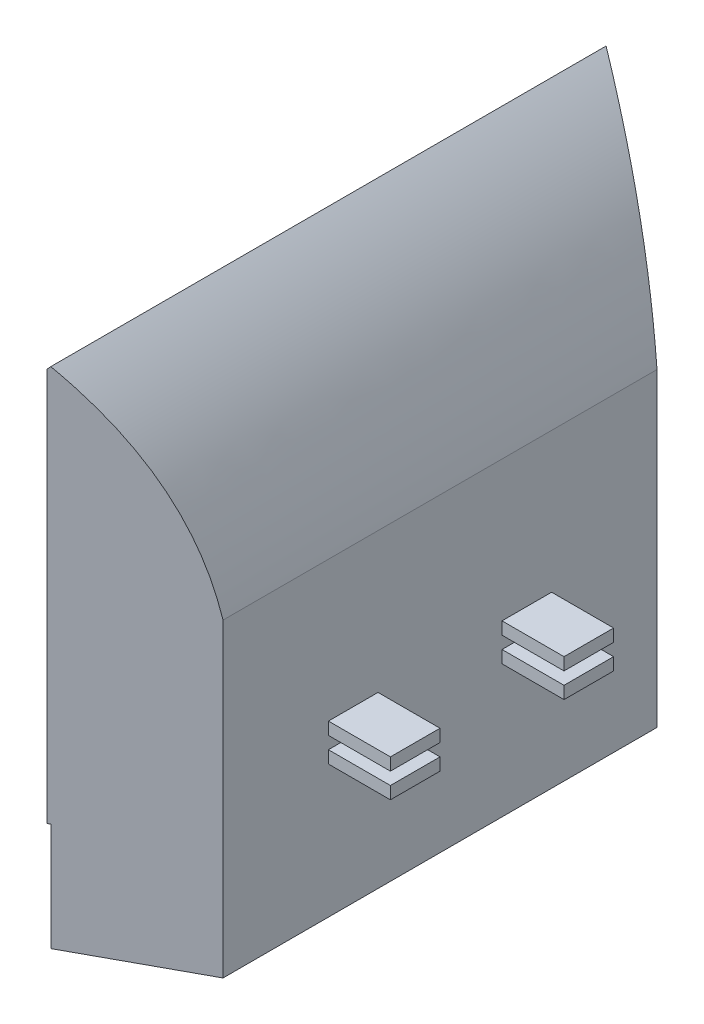
SolidWorks part; units mm, degrees
material "Pine"
ref_plane "Front Plane" through (0, 0, 0) normal (0, 0, 1) x (1, 0, 0)
ref_plane "Top Plane" through (0, 0, 0) normal (0, 1, 0) x (1, 0, 0)
ref_plane "Right Plane" through (0, 0, 0) normal (1, 0, 0) x (0, 0, -1)
sketch "Sketch1" plane through (0, 0, 0) normal (0, 0, 1) x (1, 0, 0)
  line L0 (0, 0) -> (0, -86.95)
  line L1 (0, -86.95) -> (90, -86.95)
  line L2 (90, -86.95) -> (90, 163.05)
  line L3 (3, 0) -> (3, -83.95)
  line L4 (3, -83.95) -> (87, -83.95)
  line L5 (87, -83.95) -> (87, 162.768)
  line L6 (0, 319.5362) -> (-1.9712, 317.2747)
  line L7 (0, 0) -> (3, 0)
  spline S0 degree 2 poles (90, 163.05) (72.3174, 256.4994) (0, 319.5362) knots 0 0 0 1 1 1
  spline S1 degree 1 poles (87, 162.768) (-1.9712, 317.2747) knots 0 0 1 1 construction
  spline S2 degree 3 poles (87, 162.768) (86.6353, 164.6855) (85.8667, 168.5225) (84.1938, 176.0942) (81.8385, 185.4174) (78.5926, 196.3641) (73.7046, 210.6444) (66.5448, 227.9027) (56.2723, 247.6718) (44.3168, 266.5051) (32.9484, 281.4235) (23.0079, 292.8943) (15.1298, 301.2651) (8.2091, 308.0497) (2.4655, 313.3571) (-0.4865, 315.9805) (-1.9712, 317.2747) knots 0.00149 0.00149 0.00149 0.00149 0.032694 0.063897 0.126304 0.188711 0.251118 0.375931 0.500745 0.625559 0.750373 0.812779 0.875186 0.937593 0.968797 1 1 1 1
  dimension "D4" = 184.0681
  dimension "D1" = 86.95
  dimension "D2" = 90
  dimension "D3" = 250
  dimension "D5" = 319.5362
  dimension "D6" = 3
extrude "Boss-Extrude1" add sketch "Sketch1" along normal blind 450
sketch "Sketch2" plane through (0, 0, 0) normal (0, 1, 0) x (1, 0, 0)
  line L0 (-1.9712, -450) -> (90, -400)
  line L1 (90, -450) -> (90, 0) construction
  line L2 (-1.9712, -450) -> (90, -450)
  line L3 (90, -450) -> (90, -400)
  line L4 (0, -225) -> (90, -225) construction
  line L5 (0, -450) -> (0, 0) construction
  line L6 (90, 0) -> (90, -50)
  line L7 (-1.9712, 0) -> (90, 0)
  line L8 (-1.9712, 0) -> (90, -50)
  dimension "D1" = 50
extrude "Cut-Extrude1" cut sketch "Sketch2" against normal through all both and the other way through all contours L6 L8 L7 | L3 L0 L2
sketch "Sketch3" plane through (0, 0, 0) normal (0, 1, 0) x (1, 0, 0)
  line L0 (-1.9712, -446) -> (90, -396)
  line L1 (-1.9712, -450) -> (-1.9712, 0) construction
  line L2 (90, -400) -> (90, -50) construction
  line L3 (-1.9712, -446) -> (-1.9712, -450)
  line L4 (-1.9712, -450) -> (90, -400)
  line L5 (90, -400) -> (90, -396)
  line L6 (90, -225) -> (-1.9712, -225) construction
  line L7 (-1.9712, -4) -> (-1.9712, 0)
  line L8 (90, -50) -> (90, -54)
  line L9 (-1.9712, 0) -> (90, -50)
  line L10 (-1.9712, -4) -> (90, -54)
  dimension "D1" = 4
  dimension "D2" = 4
extrude "Boss-Extrude2" add sketch "Sketch3" along normal up to next and the other way up to next
sketch "Sketch4" plane through (90, 0, 0) normal (1, 0, 0) x (0, 0, -1)
  line L0 (-225, -86.95) -> (-225, 105.8079) construction
  line L1 (-400, -86.95) -> (-50, -86.95) construction
  line L2 (-275, 30) -> (-315, 30)
  line L3 (-175, 40) -> (-135, 40)
  line L4 (-175, 40) -> (-175, 50)
  line L5 (-175, 50) -> (-135, 50)
  line L6 (-135, 40) -> (-135, 50)
  line L7 (-175, 40) -> (-135, 50) construction
  line L8 (-175, 50) -> (-135, 40) construction
  line L9 (-175, 20) -> (-135, 20)
  line L10 (-175, 20) -> (-175, 30)
  line L11 (-175, 30) -> (-135, 30)
  line L12 (-135, 20) -> (-135, 30)
  line L13 (-175, 20) -> (-135, 30) construction
  line L14 (-175, 30) -> (-135, 20) construction
  line L15 (-315, 20) -> (-315, 30)
  line L16 (-275, 20) -> (-315, 20)
  line L17 (-275, 20) -> (-275, 30)
  line L18 (-275, 50) -> (-315, 50)
  line L19 (-315, 40) -> (-315, 50)
  line L20 (-275, 40) -> (-315, 40)
  line L21 (-275, 40) -> (-275, 50)
  point P4 (-155, 45)
  point P9 (-155, 25)
  dimension "D1" = 40
  dimension "D2" = 126.95
  dimension "D3" = 10
  dimension "D4" = 50
  dimension "D5" = 10
  dimension "D6" = 40
  dimension "D7" = 50
  dimension "D8" = 10
extrude "Boss-Extrude3" add sketch "Sketch4" along normal blind 50
